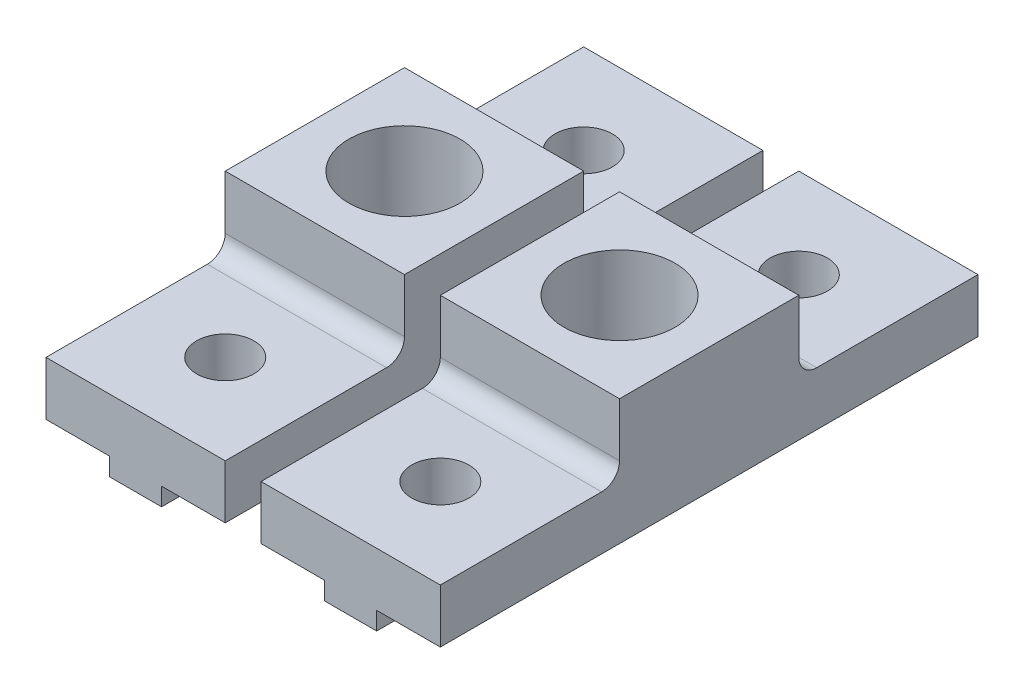
SolidWorks part; units mm, degrees
ref_plane "Front Plane" through (0, 0, 0) normal (0, 0, 1) x (1, 0, 0)
ref_plane "Top Plane" through (0, 0, 0) normal (0, 1, 0) x (1, 0, 0)
ref_plane "Right Plane" through (0, 0, 0) normal (1, 0, 0) x (0, 0, -1)
sketch "Sketch1" plane through (0, 0, 0) normal (0, 0, 1) x (1, 0, 0)
  line L0 (-5, 0) -> (5, 0)
  line L1 (5, 0) -> (5, -7)
  line L2 (5, -7) -> (1.45, -7)
  line L3 (1.45, -7) -> (1.45, -8)
  line L4 (1.45, -8) -> (-1.45, -8)
  line L5 (-1.45, -8) -> (-1.45, -7)
  line L6 (-1.45, -7) -> (-5, -7)
  line L7 (-5, -7) -> (-5, 0)
  point P2 (0, 0)
  point P9 (0, 0)
  point P11 (0, 0)
  dimension "D1" = 7
  dimension "D2" = 1
  dimension "D3" = 10
  dimension "D4" = 2.9
extrude "Boss-Extrude1" add sketch "Sketch1" along normal mid plane 30
sketch "Sketch2" plane through (0, 0, 0) normal (0, 1, 0) x (1, 0, 0)
  line L0 (5, 15) -> (-5, 15) construction
  line L1 (5, -15) -> (-5, -15) construction
  circle A0 centre (0, 0) radius 3.1
  circle A1 centre (0, 10) radius 1.6
  circle A2 centre (0, -10) radius 1.6
  point P11 (0, -15)
  point P12 (0, 0)
  dimension "D1" = 6.2
  dimension "D2" = 3.2
  dimension "D3" = 5
  dimension "D4" = 5
extrude "Cut-Extrude1" cut sketch "Sketch2" against normal through all
sketch "Sketch3" plane through (0, 0, 0) normal (0, 1, 0) x (1, 0, 0)
  line L0 (-5, -15) -> (-5, 15) construction
  line L1 (-5, 5) -> (5, 5)
  line L2 (-5, 5) -> (-5, 15)
  line L3 (-5, 15) -> (5, 15)
  line L4 (5, 5) -> (5, 15)
  line L6 (5, -15) -> (-5, -15)
  line L7 (5, -15) -> (5, -5)
  line L8 (5, -5) -> (-5, -5)
  line L9 (-5, -15) -> (-5, -5)
  dimension "D1" = 10
extrude "Cut-Extrude2" cut sketch "Sketch3" against normal blind 4
fillet "Fillet1" radius 1 2 edges at (0, -4, -5) (0, -4, 5)
pattern_linear "LPattern1" count 2 spacing 12 along (-1, 0, 0) of bodies 103
